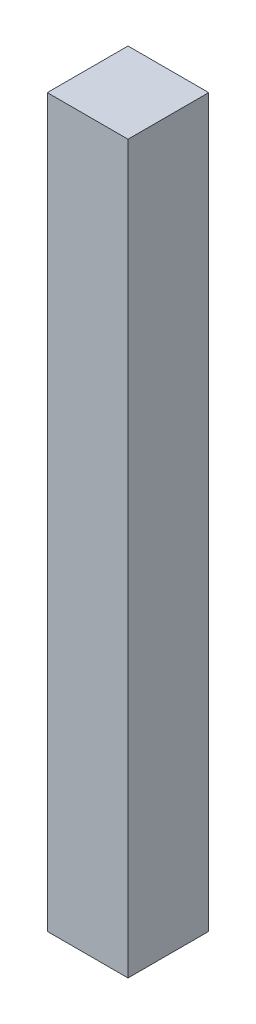
SolidWorks part; units mm, degrees
ref_plane "Plan de face" through (0, 0, 0) normal (0, 0, 1) x (1, 0, 0)
ref_plane "Plan de dessus" through (0, 0, 0) normal (0, 1, 0) x (1, 0, 0)
ref_plane "Plan de droite" through (0, 0, 0) normal (1, 0, 0) x (0, 0, -1)
sketch "Esquisse1" plane through (0, 0, 0) normal (0, 1, 0) x (1, 0, 0)
  line L1 (0, 0) -> (-20, 0)
  line L2 (0, 0) -> (0, 20)
  line L3 (0, 20) -> (-20, 20)
  line L4 (-20, 0) -> (-20, 20)
  dimension "D1" = 20
  dimension "D2" = 20
extrude "Boss.-Extru.1" add sketch "Esquisse1" along normal blind 180
